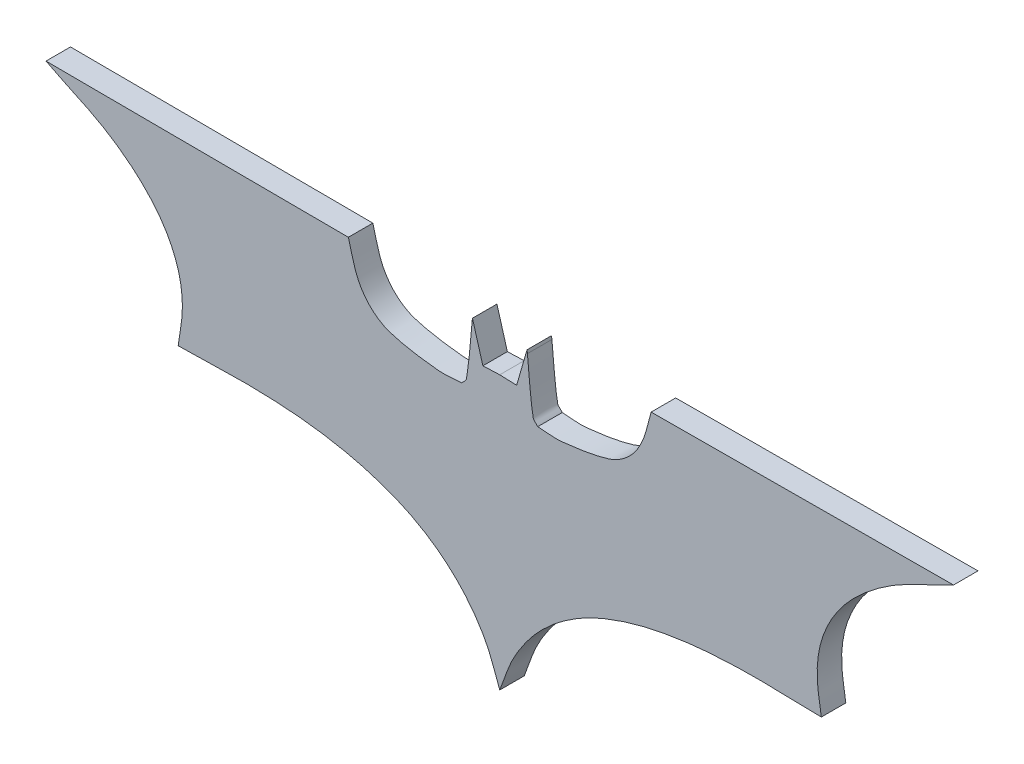
SolidWorks part; units mm, degrees
ref_plane "Ön Düzlem" through (0, 0, 0) normal (0, 0, 1) x (1, 0, 0)
ref_plane "Üst Düzlem" through (0, 0, 0) normal (0, 1, 0) x (1, 0, 0)
ref_plane "Sağ Düzlem" through (0, 0, 0) normal (1, 0, 0) x (0, 0, -1)
sketch "Sketch1" plane through (0, 0, 0) normal (0, 0, 1) x (1, 0, 0)
  line L4 (1.8602, 12.5049) -> (0, 12.5765)
  line L5 (2.8937, 16.0704) -> (1.8602, 12.5049)
  line L7 (50.0197, 17.5172) -> (16.6904, 17.3622)
  line L8 (3.0107, 16.4739) -> (3.0487, 16.122)
  line L9 (3.0107, 16.4739) -> (2.8937, 16.0704)
  line L11 (-3.0107, 16.4739) -> (-2.8937, 16.0704)
  line L12 (-3.0107, 16.4739) -> (-3.0487, 16.122)
  line L13 (-50.0197, 17.5172) -> (-16.6904, 17.3622)
  line L14 (-2.8937, 16.0704) -> (-1.8602, 12.5049)
  line L15 (-1.8602, 12.5049) -> (0, 12.5765)
  spline S0 degree 3 poles (0, -17.5172) (-0.5167, -16.2254) (-0.8932, -14.8682) (-1.5502, -13.6417) (-2.1932, -12.4414) (-2.9794, -11.3083) (-3.8755, -10.283) (-4.782, -9.2457) (-5.8112, -8.3044) (-6.9242, -7.4926) (-8.1153, -6.624) (-9.3987, -5.8644) (-10.748, -5.2707) (-12.4282, -4.5314) (-14.1821, -3.9422) (-15.967, -3.5138) (-18.0707, -3.0089) (-20.2194, -2.67) (-22.3745, -2.4803) (-25.1721, -2.234) (-27.9903, -2.1831) (-30.7972, -2.2736) (-32.347, -2.3236) (-33.8976, -2.3425) (-35.4478, -2.377) knots 0 0 0 0 1 1 1 2 2 2 3 3 3 4 4 4 5 5 5 6 6 6 7 7 7 8 8 8 8
  spline S1 degree 3 poles (-35.4478, -2.377) (-35.2928, -1.0679) (-34.9736, 0.232) (-34.9828, 1.5502) (-34.991, 2.734) (-35.1454, 3.9343) (-35.4995, 5.064) (-35.8773, 6.2695) (-36.4465, 7.4271) (-37.153, 8.4744) (-37.9242, 9.6175) (-38.8656, 10.6537) (-39.8917, 11.5748) (-41.0659, 12.6288) (-42.3566, 13.5632) (-43.7155, 14.3651) (-45.7389, 15.5592) (-47.9511, 16.4034) (-50.0197, 17.5172) knots 0 0 0 0 1 1 1 2 2 2 3 3 3 4 4 4 5 5 5 6 6 6 6
  spline S2 degree 3 poles (4.1855, 9.7146) (4.0133, 9.9385) (3.7181, 10.1082) (3.6688, 10.3863) (3.3329, 12.2798) (3.2554, 14.2101) (3.0487, 16.122) knots 0 0 0 0 1 1 1 2 2 2 2
  spline S3 degree 3 poles (16.6904, 17.3622) (16.346, 16.2254) (16.1516, 15.0318) (15.657, 13.9518) (15.2968, 13.1653) (14.792, 12.4221) (14.1585, 11.8332) (13.5418, 11.26) (12.7939, 10.7853) (11.9882, 10.5413) (10.3132, 10.0341) (8.5612, 9.7956) (6.8209, 9.6112) (5.9466, 9.5186) (5.064, 9.6801) (4.1855, 9.7146) knots 0 0 0 0 1 1 1 2 2 2 3 3 3 4 4 4 5 5 5 5
  spline S4 degree 3 poles (35.4478, -2.377) (35.2928, -1.0679) (34.9736, 0.232) (34.9828, 1.5502) (34.991, 2.734) (35.1454, 3.9343) (35.4995, 5.064) (35.8773, 6.2695) (36.4465, 7.4271) (37.153, 8.4744) (37.9242, 9.6175) (38.8656, 10.6537) (39.8917, 11.5748) (41.0659, 12.6288) (42.3566, 13.5632) (43.7155, 14.3651) (45.7389, 15.5592) (47.9511, 16.4034) (50.0197, 17.5172) knots 0 0 0 0 1 1 1 2 2 2 3 3 3 4 4 4 5 5 5 6 6 6 6
  spline S5 degree 3 poles (-16.6904, 17.3622) (-16.346, 16.2254) (-16.1516, 15.0318) (-15.657, 13.9518) (-15.2968, 13.1653) (-14.792, 12.4221) (-14.1585, 11.8332) (-13.5418, 11.26) (-12.7939, 10.7853) (-11.9882, 10.5413) (-10.3132, 10.0341) (-8.5612, 9.7956) (-6.8209, 9.6112) (-5.9466, 9.5186) (-5.064, 9.6801) (-4.1855, 9.7146) knots 0 0 0 0 1 1 1 2 2 2 3 3 3 4 4 4 5 5 5 5
  spline S6 degree 3 poles (-4.1855, 9.7146) (-4.0133, 9.9385) (-3.7181, 10.1082) (-3.6688, 10.3863) (-3.3329, 12.2798) (-3.2554, 14.2101) (-3.0487, 16.122) knots 0 0 0 0 1 1 1 2 2 2 2
  spline S7 degree 3 poles (0, -17.5172) (0.5167, -16.2254) (0.8932, -14.8682) (1.5502, -13.6417) (2.1932, -12.4414) (2.9794, -11.3083) (3.8755, -10.283) (4.782, -9.2457) (5.8112, -8.3044) (6.9242, -7.4926) (8.1153, -6.624) (9.3987, -5.8644) (10.748, -5.2707) (12.4282, -4.5314) (14.1821, -3.9422) (15.967, -3.5138) (18.0707, -3.0089) (20.2194, -2.67) (22.3745, -2.4803) (25.1721, -2.234) (27.9903, -2.1831) (30.7972, -2.2736) (32.347, -2.3236) (33.8976, -2.3425) (35.4478, -2.377) knots 0 0 0 0 1 1 1 2 2 2 3 3 3 4 4 4 5 5 5 6 6 6 7 7 7 8 8 8 8
extrude "Boss-Extrude4" add sketch "Sketch1" along normal blind 2.7
